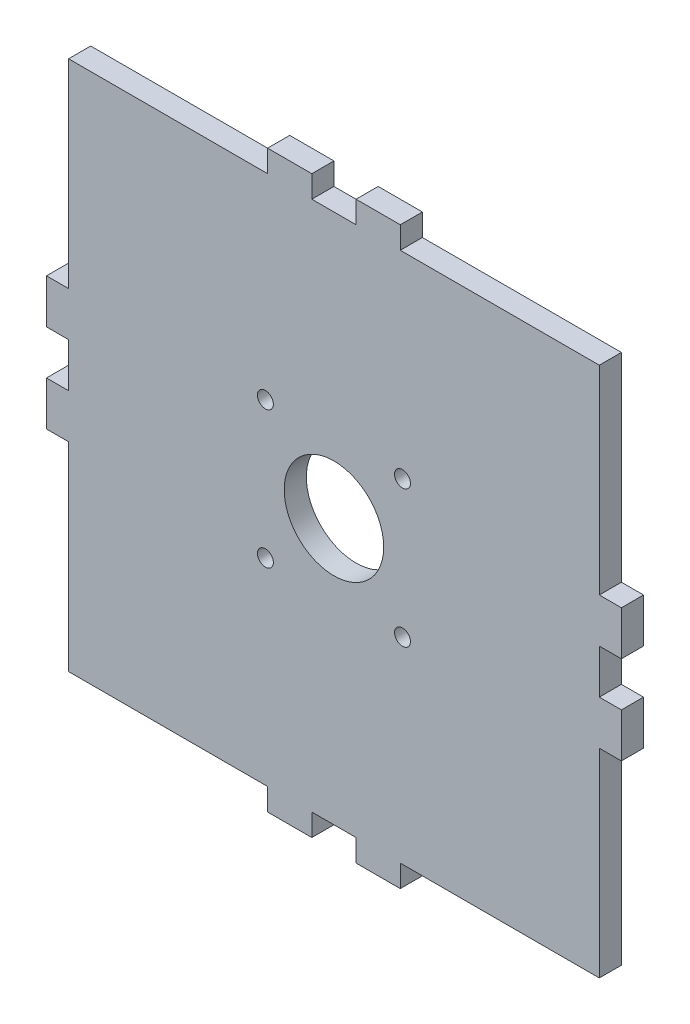
SolidWorks part; units mm, degrees
ref_plane "Front Plane" through (0, 0, 0) normal (0, 0, 1) x (1, 0, 0)
ref_plane "Top Plane" through (0, 0, 0) normal (0, 1, 0) x (1, 0, 0)
ref_plane "Right Plane" through (0, 0, 0) normal (1, 0, 0) x (0, 0, -1)
sketch "Sketch1" plane through (0, 0, 0) normal (0, 0, 1) x (1, 0, 0)
  line L0 (0, 0) -> (0, 93.8767) construction
  line L1 (0, 0) -> (-161.7495, 0) construction
  line L2 (5, 60) -> (-5, 60)
  line L3 (-5, 60) -> (-5, 65)
  line L4 (-5, 65) -> (-15, 65)
  line L5 (-15, 65) -> (-15, 60)
  line L6 (-15, 60) -> (-60, 60)
  line L7 (-60, 60) -> (-60, 15)
  line L8 (-60, 15) -> (-65, 15)
  line L9 (-65, 15) -> (-65, 5)
  line L10 (-65, 5) -> (-60, 5)
  line L11 (-60, 5) -> (-60, -5)
  line L12 (60, 5) -> (60, -5)
  line L13 (65, 5) -> (60, 5)
  line L14 (65, 15) -> (65, 5)
  line L15 (60, 15) -> (65, 15)
  line L16 (60, 60) -> (60, 15)
  line L17 (15, 60) -> (60, 60)
  line L18 (15, 65) -> (15, 60)
  line L19 (5, 65) -> (15, 65)
  line L20 (5, 60) -> (5, 65)
  line L21 (5, -60) -> (5, -65)
  line L22 (5, -65) -> (15, -65)
  line L23 (15, -65) -> (15, -60)
  line L24 (15, -60) -> (60, -60)
  line L25 (60, -60) -> (60, -15)
  line L26 (60, -15) -> (65, -15)
  line L27 (65, -15) -> (65, -5)
  line L28 (65, -5) -> (60, -5)
  line L29 (-65, -5) -> (-60, -5)
  line L30 (-65, -15) -> (-65, -5)
  line L31 (-60, -15) -> (-65, -15)
  line L32 (-60, -60) -> (-60, -15)
  line L33 (-15, -60) -> (-60, -60)
  line L34 (-15, -65) -> (-15, -60)
  line L35 (-5, -65) -> (-15, -65)
  line L36 (-5, -60) -> (-5, -65)
  line L37 (5, -60) -> (-5, -60)
  circle A0 centre (0, 0) radius 11.25
  circle A1 centre (-15.5, 15.5) radius 1.8
  circle A2 centre (15.5, 15.5) radius 1.8
  circle A3 centre (15.5, -15.5) radius 1.8
  circle A4 centre (-15.5, -15.5) radius 1.8
  point P13 (-62.5, 5)
  point P16 (-37.5, 60)
  point P27 (0, 60)
  point P36 (60, 0)
  point P37 (-60, 0)
  point P45 (0, -60)
  dimension "D11" = 15.5
  dimension "D1" = 60
  dimension "D2" = 60
  dimension "D3" = 60
  dimension "D4" = 5
  dimension "D5" = 5
  dimension "D6" = 5
  dimension "D7" = 10
  dimension "D8" = 5
  dimension "D9" = 10
  dimension "D10" = 5
  dimension "D12" = 15.5
extrude "Boss-Extrude1" add sketch "Sketch1" along normal blind 5
